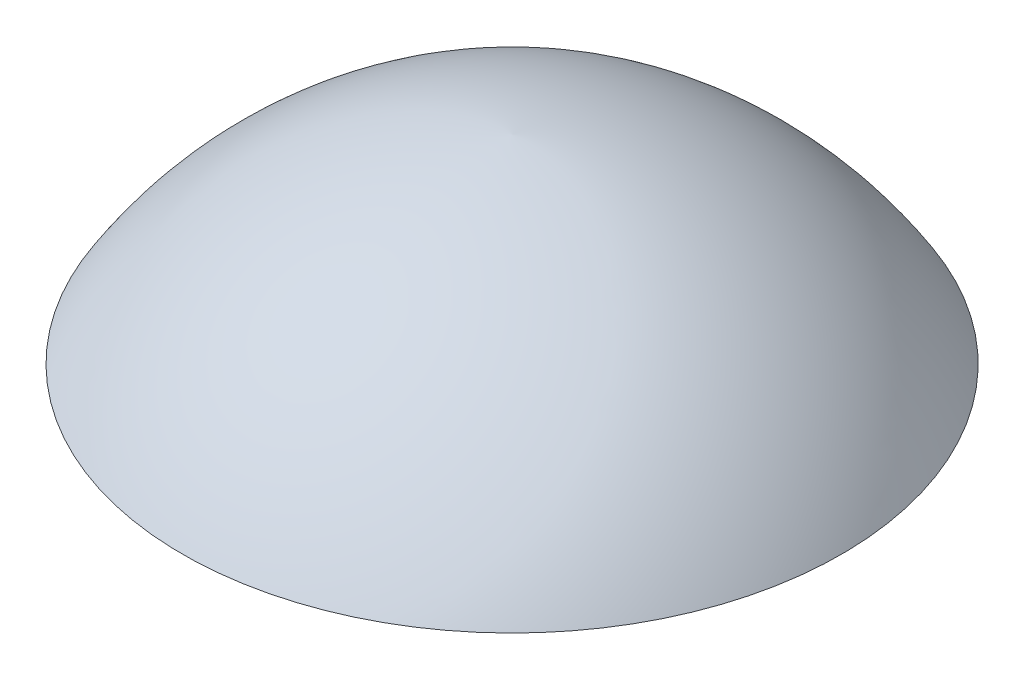
SolidWorks part; units mm, degrees
ref_plane "Ön Düzlem" through (0, 0, 0) normal (0, 0, 1) x (1, 0, 0)
ref_plane "Üst Düzlem" through (0, 0, 0) normal (0, 1, 0) x (1, 0, 0)
ref_plane "Sağ Düzlem" through (0, 0, 0) normal (1, 0, 0) x (0, 0, -1)
sketch "Çizim1" plane through (0, 0, 0) normal (0, 1, 0) x (1, 0, 0)
  circle A0 centre (0, 0) radius 16.5
sketch "Çizim2" plane through (0, 0, 0) normal (0, 0, 1) x (1, 0, 0)
  line L0 (0, 0) -> (0, 9.9493)
  line L1 (16.5, 0) -> (-16.5, 0) construction
  line L2 (0, -18.15) -> (0, 18.15) construction
  line L3 (0, 0) -> (-16.5, 0)
  arc A0 (-16.5, 0) -> (0, 9.9493) centre (1.3361, -10.9231) cw
revolve "Döndür1" add sketch "Çizim2" angle 360 about L0
